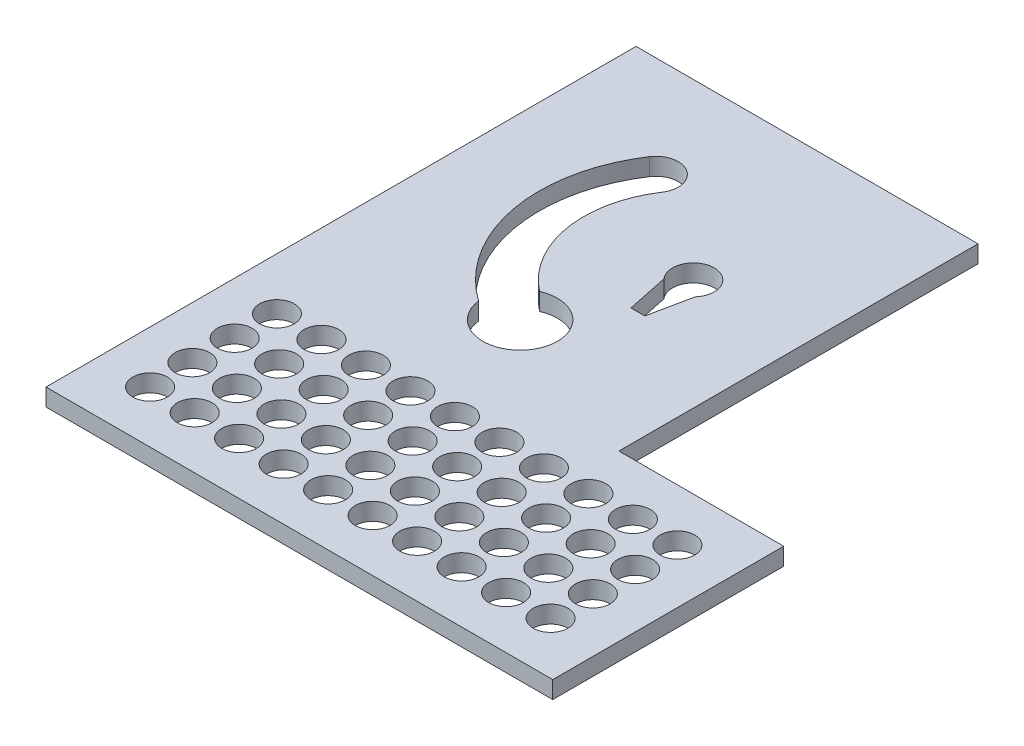
SolidWorks part; units mm, degrees
ref_plane "Ön Düzlem" through (0, 0, 0) normal (0, 0, 1) x (1, 0, 0)
ref_plane "Üst Düzlem" through (0, 0, 0) normal (0, 1, 0) x (1, 0, 0)
ref_plane "Sağ Düzlem" through (0, 0, 0) normal (1, 0, 0) x (0, 0, -1)
sketch "Çizim1" plane through (0, 0, 0) normal (0, 1, 0) x (1, 0, 0)
  line L1 (0, 0) -> (73, 0)
  line L2 (0, 0) -> (0, 85)
  line L3 (0, 85) -> (73, 85)
  line L4 (73, 0) -> (73, 85)
  line L6 (49.2622, 85) -> (49.25, 33.28)
  line L7 (49.25, 33.28) -> (73, 33.2744)
  dimension "D1" = 73
  dimension "D2" = 23.75
  dimension "D3" = 51.72
  dimension "D4" = 85
extrude "Yükseklik-Ekstrüzyon1" add sketch "Çizim1" along normal blind 2.5 contours L7 L6 L3 L2 L1 L4
sketch "Çizim2" plane through (0, 0, 0) normal (0, -1, 0) x (1, 0, 0)
  line L0 (32.2628, -52) -> (34.2628, -52)
  line L1 (34.2628, -52) -> (35.5128, -58.0157)
  line L2 (32.2628, -52) -> (31.0128, -58.0157)
  circle A0 centre (33.2628, -60) radius 2.5
  arc A1 (31.0128, -58.0157) -> (35.5128, -58.0157) centre (33.2628, -60) ccw
  point P19 (33.2628, -52)
  dimension "D1" = 5
  dimension "D4" = 3
  dimension "D2" = 8
  dimension "D3" = 2
  dimension "D5" = 4.5
  dimension "D6" = 6.0157
extrude "Kes-Ekstrüzyon1" cut sketch "Çizim2" against normal through all contours L2 A1 L1 L0 A0 | A0
sketch "Çizim3" plane through (0, 0, 0) normal (0, -1, 0) x (1, 0, 0)
  circle A0 centre (25.7568, -42.5455) radius 5.375
  arc A2 (25.7568, -42.5455) -> (17.4048, -70.4654) centre (33.2628, -60) ccw construction
  arc A3 (24.4926, -39.6058) -> (14.734, -72.2281) centre (33.2628, -60) ccw
  arc A4 (27.0209, -45.4852) -> (20.0756, -68.7028) centre (33.2628, -60) ccw
  arc A5 (27.0209, -45.4852) -> (24.4926, -39.6058) centre (25.7568, -42.5455) ccw
  arc A6 (14.734, -72.2281) -> (20.0756, -68.7028) centre (17.4048, -70.4654) ccw
  point P7 (15.0597, -54.5548)
  dimension "D1" = 3.2
  dimension "D2" = 10.75
  dimension "D3" = 19
extrude "Kes-Ekstrüzyon2" cut sketch "Çizim3" against normal through all contours A3 A6 A4 A0 | A4 A5 A3 A0 | A5 A4 A0 A3
sketch "Çizim5" plane through (0, 0, 0) normal (0, -1, 0) x (1, 0, 0)
  line L0 (0, -33.28) -> (49.25, -33.28)
  line L1 (49.2494, -28.28) -> (68, -28.2756)
  line L2 (68, -28.2756) -> (68, -5)
  line L3 (68, -5) -> (5, -5)
  line L4 (5, -5) -> (5, -28.28)
  line L5 (5, -28.28) -> (49.2494, -28.28)
  line L6 (49.25, -33.28) -> (73, -33.2744)
  line L7 (73, -33.2744) -> (73, 0)
  line L8 (73, 0) -> (0, 0)
  line L9 (0, 0) -> (0, -85)
  line L10 (0, -85) -> (49.2622, -85)
  line L11 (49.2622, -85) -> (49.25, -33.28)
  line L12 (49.25, -33.28) -> (73, -33.2744)
  line L13 (73, -33.2744) -> (73, 0)
  line L14 (73, 0) -> (0, 0)
  line L15 (0, 0) -> (0, -33.28)
  circle A0 centre (7.5, -7.5) radius 2.5
  circle A65 centre (13.91, -7.5) radius 2.5
  circle A66 centre (20.32, -7.5) radius 2.5
  circle A67 centre (26.73, -7.5) radius 2.5
  circle A68 centre (33.14, -7.5) radius 2.5
  circle A69 centre (39.55, -7.5) radius 2.5
  circle A70 centre (45.96, -7.5) radius 2.5
  circle A71 centre (52.37, -7.5) radius 2.5
  circle A72 centre (58.78, -7.5) radius 2.5
  circle A73 centre (65.19, -7.5) radius 2.5
  circle A74 centre (13.91, -13.59) radius 2.5
  circle A75 centre (20.32, -13.59) radius 2.5
  circle A76 centre (26.73, -13.59) radius 2.5
  circle A77 centre (33.14, -13.59) radius 2.5
  circle A78 centre (39.55, -13.59) radius 2.5
  circle A79 centre (45.96, -13.59) radius 2.5
  circle A80 centre (52.37, -13.59) radius 2.5
  circle A81 centre (58.78, -13.59) radius 2.5
  circle A82 centre (65.19, -13.59) radius 2.5
  circle A83 centre (13.91, -19.68) radius 2.5
  circle A84 centre (20.32, -19.68) radius 2.5
  circle A85 centre (26.73, -19.68) radius 2.5
  circle A86 centre (33.14, -19.68) radius 2.5
  circle A87 centre (39.55, -19.68) radius 2.5
  circle A88 centre (45.96, -19.68) radius 2.5
  circle A89 centre (52.37, -19.68) radius 2.5
  circle A90 centre (58.78, -19.68) radius 2.5
  circle A91 centre (65.19, -19.68) radius 2.5
  circle A92 centre (13.91, -25.77) radius 2.5
  circle A93 centre (20.32, -25.77) radius 2.5
  circle A94 centre (26.73, -25.77) radius 2.5
  circle A95 centre (33.14, -25.77) radius 2.5
  circle A96 centre (39.55, -25.77) radius 2.5
  circle A97 centre (45.96, -25.77) radius 2.5
  circle A98 centre (52.37, -25.77) radius 2.5
  circle A99 centre (58.78, -25.77) radius 2.5
  circle A100 centre (65.19, -25.77) radius 2.5
  circle A101 centre (7.5, -13.59) radius 2.5
  circle A102 centre (7.5, -19.68) radius 2.5
  circle A103 centre (7.5, -25.77) radius 2.5
  dimension "D3" = 5
  dimension "D1" = 0
  dimension "D2" = 5
  dimension "D4" = 10
  dimension "D5" = 4
extrude "Kes-Ekstrüzyon3" cut sketch "Çizim5" against normal blind 10 contours A0 | A65 | A66 | A75 | A74 | A101 | A102 | A83 | A103 | A92 | A93 | A84 | A85 | A86 | A87 | A88 | A97 | A96 | A95 | A94 | A98 | A90 | A89 | A91 | A100 | A82 | A81 | A80 | A73 | A72 | A71 | A70 | A79 | A78 | A69 | A77 | A68 | A67 | A76 | A99
